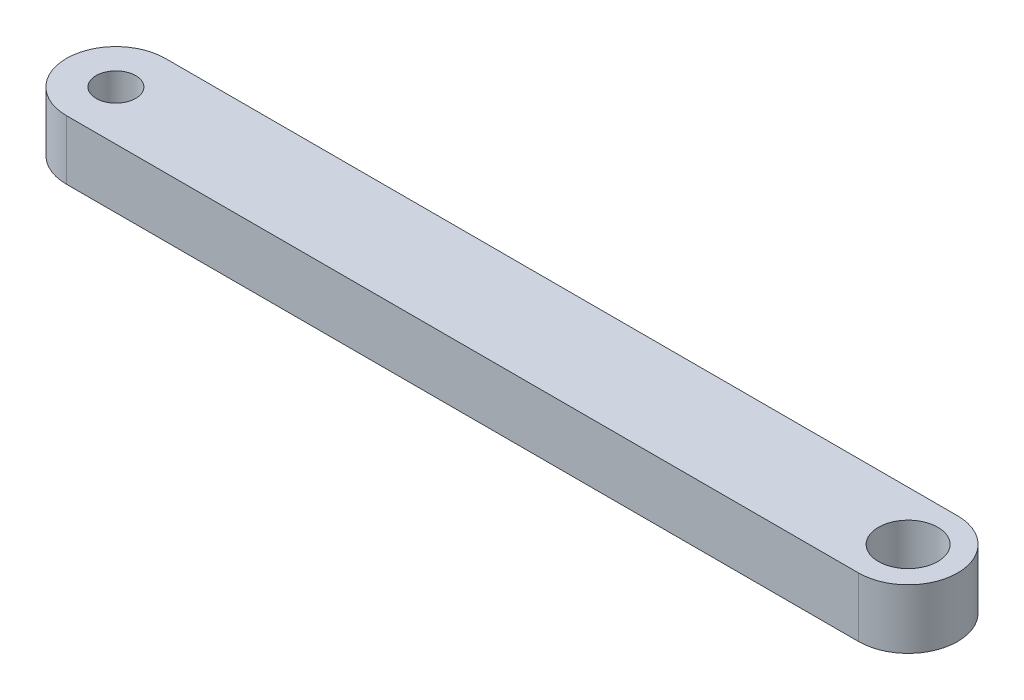
SolidWorks part; units mm, degrees
ref_plane "Front Plane" through (0, 0, 0) normal (0, 0, 1) x (1, 0, 0)
ref_plane "Top Plane" through (0, 0, 0) normal (0, 1, 0) x (1, 0, 0)
ref_plane "Right Plane" through (0, 0, 0) normal (1, 0, 0) x (0, 0, -1)
ref_plane "Plane1" through (0, 0, 0) normal (0, -1, 0) x (1, 0, 0)
sketch "Sketch1" plane through (0, 0, 0) normal (0, -1, 0) x (1, 0, 0)
  line L0 (31, 2.5) -> (-9, 2.5)
  line L1 (-9, -2.5) -> (31, -2.5)
  line L2 (28.3996, -1.0193) -> (27.9997, 0.0008) construction
  line L3 (-9.6889, 8.4389) -> (-1.6698, -4.2377) construction
  line L4 (28.3996, -1.0193) -> (28.3995, -1.0194) construction
  arc A0 (-9, 2.5) -> (-9, -2.5) centre (-9, 0) ccw
  arc A1 (31, -2.5) -> (31, 2.5) centre (31, 0) ccw
  circle A2 centre (31, 0) radius 1.5
  circle A3 centre (-9, 0) radius 1
  point P9 (-11.5, 0)
  point P10 (33.5, 0)
  point P18 (52.9209, -8.4622)
  dimension "D1" = 2
  dimension "D2" = 3
  dimension "D3" = 2.5
  dimension "D4" = 41
  dimension "D5" = 9
extrude "Boss-Extrude1" add sketch "Sketch1" against normal blind 3
